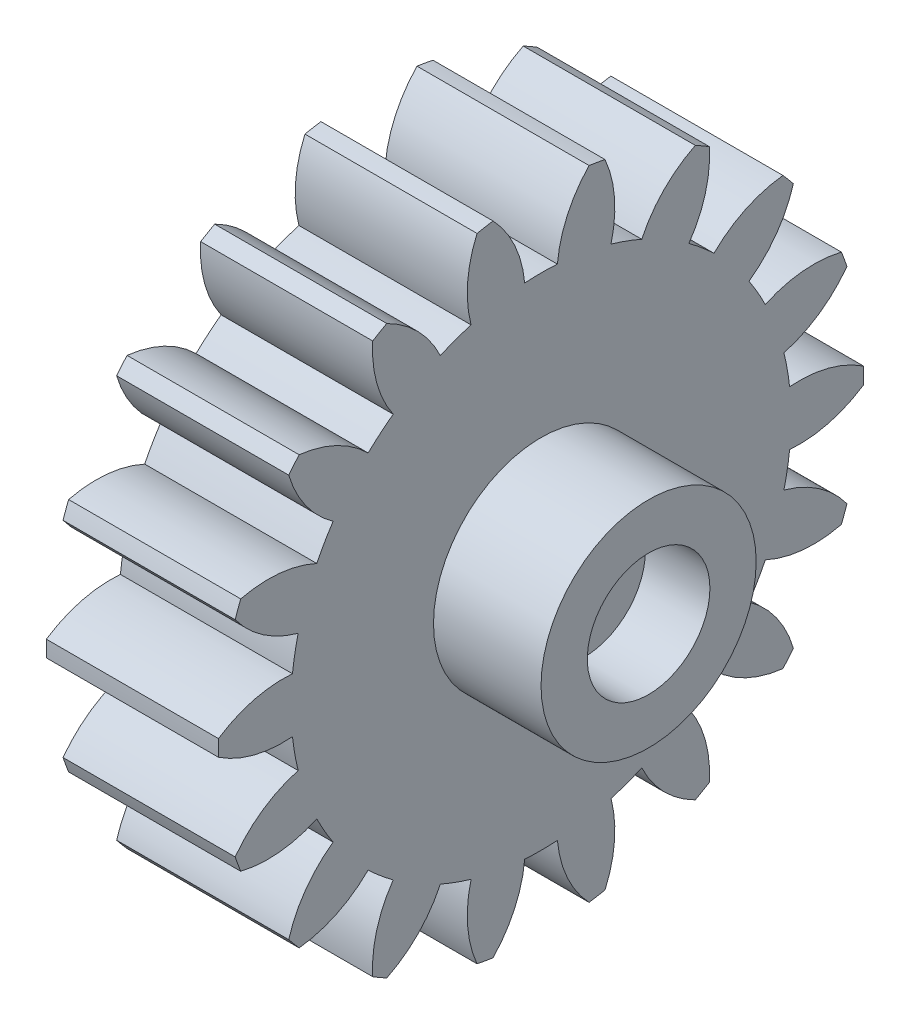
SolidWorks part; units mm, degrees
ref_plane "Plane1" through (0, 0, 0) normal (0, 0, 1) x (1, 0, 0)
ref_plane "Plane2" through (0, 0, 0) normal (0, 1, 0) x (1, 0, 0)
ref_plane "Plane3" through (0, 0, 0) normal (1, 0, 0) x (0, 0, -1)
sketch "HoldingSke" plane through (0, 0, 0) normal (0, 1, 0) x (1, 0, 0)
  line L0 (0, 0) -> (0.634, -0.206)
  line L1 (-15, 0) -> (100, 0) construction
  line L2 (0, 0) -> (-2.1039, 2.3779)
  line L3 (0, 0) -> (-11.863, 4.5341)
  line L4 (0, 0) -> (8.2133, 2.6687)
  line L5 (0, 0) -> (-46.8476, -17.4728)
  line L6 (0, 0) -> (-6.6317, -4.4744)
  line L7 (-2.1039, 2.3779) -> (8.6586, 51.2059)
  line L8 (-76.2, 54.61) -> (-76.1, 54.61)
  line L9 (-71.009, 38.7566) -> (-53.1078, 45.2721)
  line L10 (-76.2, 71.12) -> (104.1128, 71.12)
  line L11 (0, 0) -> (-8, 0)
  line L12 (-76.2, 101.6) -> (-76.147, 101.6)
  line L13 (24.9733, 27.94) -> (52.9518, 28.4284)
  line L14 (24.9733, 27.94) -> (24.9743, 27.94)
  line L15 (24.9733, 27.94) -> (100.4006, 29.5858)
  line L16 (-63.627, -1.5) -> (-12.827, -1.5)
  circle A0 centre (0, 0) radius 0.4
  circle A1 centre (0, 0) radius 11.624
  circle A2 centre (0, 0) radius 37.5
  circle A3 centre (0, 0) radius 0.4
  dimension "MHD" = 23.248
  dimension "Hub_dia" = 75
  dimension "Bore" = 0.8
  dimension "MBD" = 0.8
  dimension "Num_teeth" = 18
  dimension "Pitch" = 0.6667
  dimension "Overall_len" = 50
  dimension "Show_teeth" = 18
  dimension "Thickness" = 8
  dimension "OAL" = 50.0001
  dimension "T_dim" = 0.1
  dimension "Ap" = 20
  dimension "H" = 19.05
  dimension "Pitch_radius" = 180.3128
  dimension "Width" = 8
  dimension "Backlash" = 0.053
  dimension "Addendum_fac" = 1
  dimension "Dedendum_fac" = 1.25
  dimension "Clearance_fac" = 0.25
  dimension "Dedendum_add" = 0.001
  dimension "Module" = 1.5
sketch "BasProSke" plane through (0, 0, 0) normal (0, 1, 0) x (1, 0, 0)
  line L0 (-10, 0) -> (60, 0) construction
  line L1 (0, 0) -> (0, 15)
  line L2 (0, 0) -> (8, 0)
  line L3 (8, 0) -> (8, 15)
  line L4 (8, 15) -> (0, 15)
  dimension "Thickness" = 8
  dimension "Diameter" = 30
revolve "Base-Revolve" add sketch "BasProSke" angle 360 about L0
sketch "TooCutSke" plane through (0, 0, 0) normal (1, 0, 0) x (0, 0, -1)
  line L1 (0, 0) -> (0, 107) construction
  line L2 (0, 0) -> (-1.2693, 13.4402) construction
  line L3 (0, 0) -> (-4.6734, 26.504) construction
  line L4 (-1.2693, 13.4402) -> (-2.3367, 13.252) construction
  arc A0 (0.76, 11.5991) -> (-0.76, 11.5991) centre (0, 0) ccw
  arc A1 (2.2542, 14.8553) -> (-2.2542, 14.8553) centre (0, 0) ccw
  circle A2 centre (0, 0) radius 13.5 construction
  circle A3 centre (0, 0) radius 12.6859 construction
  arc A4 (-0.76, 11.5991) -> (-2.2542, 14.8553) centre (-6.1371, 11.1026) ccw
  arc A5 (2.2542, 14.8553) -> (0.76, 11.5991) centre (6.1371, 11.1026) ccw
  dimension "Root_dia" = 23.248
  dimension "Overcut_dia" = 30.0508
  dimension "Pitch_dia" = 27
  dimension "Base_dia" = 25.3717
  dimension "Flank_rad" = 5.4
  dimension "Half_ang" = 10
  dimension "Half_CT" = 1.0839
extrude "ToothCut" cut sketch "TooCutSke" along normal through all
fillet "Breaks" [suppressed] radius 0.03
fillet "RootFillets" [suppressed] radius 0.376
pattern_circular "TeethCuts" count 18 every 20 about axis through (-10, 0, 0) along (1, 0, 0) of "ToothCut", "RootFillets", "Breaks"
sketch "HubNeaOneSke" plane through (0, 0, 0) normal (-1, 0, 0) x (0, 0, 1)
  circle A0 centre (0, 0) radius 11.624
  dimension "Diameter" = 23.248
extrude "HubNearOne" [suppressed] add sketch "HubNeaOneSke" along normal blind 42.0001
sketch "HubNeaBotSke" plane through (0, 0, 0) normal (-1, 0, 0) x (0, 0, 1)
  circle A0 centre (0, 0) radius 11.624
  dimension "Diameter" = 23.248
extrude "HubNearBoth" [suppressed] add sketch "HubNeaBotSke" along normal blind 21
ref_plane "FarPln" through (8, 0, 0) normal (1, 0, 0) x (0, 0, -1)
sketch "HubFarSke" plane through (8, 0, 0) normal (1, 0, 0) x (0, 0, -1)
  circle A0 centre (0, 0) radius 11.624
  dimension "Diameter" = 23.248
extrude "HubFar" [suppressed] add sketch "HubFarSke" along normal blind 21
sketch "BorSke" plane through (0, 0, 0) normal (1, 0, 0) x (0, 0, -1)
  circle A0 centre (0, 0) radius 0.4
  dimension "Diameter" = 0.8
extrude "Bore" cut sketch "BorSke" along normal mid plane 100.0001
sketch "KeySke" plane through (0, 0, 0) normal (1, 0, 0) x (0, 0, -1)
  line L0 (-0.05, 0) -> (-0.05, 0.5)
  line L1 (-0.05, 0.5) -> (0.05, 0.5)
  line L2 (0.05, 0.5) -> (0.05, 0)
  line L3 (0, 0) -> (0, 34) construction
  line L4 (-0.05, 0) -> (0.05, 0)
  dimension "Offset" = 0.5
  dimension "Width" = 0.1
extrude "Keyway" [suppressed] cut sketch "KeySke" along normal mid plane 100.0001
pattern_circular "Keyway2" [suppressed] count 2 every 90 about axis through (-10, 0, 0) along (1, 0, 0)
sketch "Esquisse1" plane through (8, 0, 0) normal (1, 0, 0) x (0, 0, -1)
  circle A0 centre (0, 0) radius 5
  dimension "D1" = 10
extrude "Boss.-Extru.1" add sketch "Esquisse1" along normal blind 5
sketch "Esquisse2" plane through (13, 0, 0) normal (1, 0, 0) x (0, 0, -1)
  circle A0 centre (0, 0) radius 2.85
  dimension "D1" = 5.7
extrude "Enlèv. mat.-Extru.1" cut sketch "Esquisse2" against normal blind 3
sketch "Esquisse3" plane through (10, 0, 0) normal (1, 0, 0) x (0, 0, -1)
  circle A0 centre (0, 0) radius 1
  dimension "D1" = 2
extrude "Enlèv. mat.-Extru.2" cut sketch "Esquisse3" against normal through all
equation "' \"Module@HoldingSke\" = 6.35"
equation "' \"Num_teeth@HoldingSke\" = 12"
equation "' \"Ap@HoldingSke\" =  20"
equation "' \"Ap@HoldingSke\" = 20"
equation "' \"Width@HoldingSke\" = 0.5 * 25.4"
equation "' \"Hub_dia@HoldingSke\"= 1 * 25.4"
equation "' \"Hub_dia@HoldingSke\" = 1 * 25.4"
equation "' \"Overall_len@HoldingSke\" = 1.0 * 25.4"
equation "' \"Bore@HoldingSke\" = 0.75 * 25.4"
equation "' \"T_dim@HoldingSke\" = 0.1 * 25.4"
equation "' \"Width@KeySke\" = 0.25 * 25.4"
equation "' \"Show_teeth@HoldingSke\" = 13"
equation "' \"Backlash@HoldingSke\" = 0.009 * 25.4"
equation "' \"Addendum_fac@HoldingSke\" = 1.0"
equation "' \"Dedendum_fac@HoldingSke\" = 1.25"
equation "' \"Dedendum_add@HoldingSke\" = 0.00005 * 25.4"
equation "' \"Clearance_fac@HoldingSke\" = 0.25"
equation "\"Pitch@HoldingSke\" = 1 / \"Module@HoldingSke\""
equation "\"Overcut_dia@TooCutSke\" = (\"Num_teeth@HoldingSke\" + 2 * \"Addendum_fac@HoldingSke\") / \"Pitch@HoldingSke\" + 0.002 * 25.4"
equation "\"Pitch_dia@TooCutSke\" = \"Num_teeth@HoldingSke\" / \"Pitch@HoldingSke\""
equation "\"Base_dia@TooCutSke\" = \"Num_teeth@HoldingSke\" / \"Pitch@HoldingSke\" * cos((\"Ap@HoldingSke\"  * 3.14159265 / 180))"
equation "\"Root_dia@TooCutSke\" = (\"Num_teeth@HoldingSke\" + 2) / \"Pitch@HoldingSke\" - 2 * (\"Addendum_fac@HoldingSke\" + \"Dedendum_fac@HoldingSke\") / \"Pitch@HoldingSke\" - \"Dedendum_add@HoldingSke\" * 2"
equation "\"Half_ang@TooCutSke\" = 180 / \"Num_teeth@HoldingSke\""
equation "\"Half_CT@TooCutSke\" = \"Num_teeth@HoldingSke\" / \"Pitch@HoldingSke\" * sin((3.14159265 / 2 / \"Num_teeth@HoldingSke\")) / 2 - 7 * \"Backlash@HoldingSke\" / 4"
equation "\"Flank_rad@TooCutSke\" = \"Num_teeth@HoldingSke\" / \"Pitch@HoldingSke\" / 5"
equation "\"Radius@RootFillets\" = \"Clearance_fac@HoldingSke\" / \"Pitch@HoldingSke\" + \"Dedendum_add@HoldingSke\""
equation "\"Break_rad@Breaks\" = 0.02 / \"Pitch@HoldingSke\""
equation "\"Thickness@HoldingSke\" = \"Width@HoldingSke\""
equation "\"OAL@HoldingSke\" = \"Thickness@HoldingSke\""
equation "\"MHD@HoldingSke\" = (\"Num_teeth@HoldingSke\" + 2) / \"Pitch@HoldingSke\" - 2 * (\"Addendum_fac@HoldingSke\" + \"Dedendum_fac@HoldingSke\")  / \"Pitch@HoldingSke\" - \"Dedendum_add@HoldingSke\" * 2"
equation "\"MBD@HoldingSke\" = (\"Num_teeth@HoldingSke\" + 2) / \"Pitch@HoldingSke\" - 2 * (\"Addendum_fac@HoldingSke\" + \"Dedendum_fac@HoldingSke\")  / \"Pitch@HoldingSke\" - \"Dedendum_add@HoldingSke\" * 2 - 0.002 * 25.4"
equation "\"MHD@HoldingSke\" = ((sgn( \"MHD@HoldingSke\" - \"Hub_dia@HoldingSke\" )-1)*( \"MHD@HoldingSke\" - \"Hub_dia@HoldingSke\" ))/-2+ \"Hub_dia@HoldingSke\""
equation "\"MBD@HoldingSke\" = ((sgn( \"MBD@HoldingSke\" - \"Bore@HoldingSke\" )-1)*( \"MBD@HoldingSke\" - \"Bore@HoldingSke\" ))/-2+ \"Bore@HoldingSke\""
equation "\"OAL@HoldingSke\" = ((sgn( \"OAL@HoldingSke\" - \"Overall_len@HoldingSke\" )+1)*( \"OAL@HoldingSke\" - \"Overall_len@HoldingSke\" ))/2 + \"Overall_len@HoldingSke\" + 0.000002 * 25.4"
equation "\"Num_teeth@TeethCuts\" = int( \"Show_teeth@HoldingSke\" ) + 1"
equation "\"Num_teeth@TeethCuts\" = ((sgn( \"Num_teeth@TeethCuts\" - \"Num_teeth@HoldingSke\" )-1)*( \"Num_teeth@TeethCuts\" - \"Num_teeth@HoldingSke\" ))/-2+ \"Num_teeth@HoldingSke\""
equation "\"Num_teeth@TeethCuts\" = ((sgn( \"Num_teeth@TeethCuts\" - 2.0)+1)*( \"Num_teeth@TeethCuts\" - 2.0))/2 +2.0"
equation "\"Angle@TeethCuts\" = 360.0 / \"Num_teeth@HoldingSke\""
equation "\"Diameter@BasProSke\" = (\"Num_teeth@HoldingSke\" + 2 * \"Addendum_fac@HoldingSke\") / \"Pitch@HoldingSke\""
equation "\"Thickness@BasProSke\"  = \"Thickness@HoldingSke\""
equation "' \"Fillet_rad@BasProSke\" =  \"Thickness@HoldingSke\" * 0.05"
equation "' \"Fillet_rad@BasProSke\" = \"Thickness@HoldingSke\" * 0.05"
equation "\"MHD@HoldingSke\" = ((sgn( \"MHD@HoldingSke\" - \"Root_dia@TooCutSke\" )-1)*( \"MHD@HoldingSke\" - \"Root_dia@TooCutSke\" ))/-2+ \"Root_dia@TooCutSke\""
equation "\"Diameter@HubNeaOneSke\" = \"MHD@HoldingSke\""
equation "\"Length@HubNearOne\" = \"OAL@HoldingSke\" - \"Thickness@BasProSke\""
equation "\"Diameter@HubNeaBotSke\" = \"MHD@HoldingSke\""
equation "\"Length@HubNearBoth\" = ( \"OAL@HoldingSke\" - \"Thickness@BasProSke\" ) / 2.0"
equation "\"Thickness@FarPln\" = \"Thickness@BasProSke\""
equation "\"Diameter@HubFarSke\" = \"MHD@HoldingSke\""
equation "\"Length@HubFar\" = ( \"OAL@HoldingSke\" - \"Thickness@BasProSke\" ) / 2.0"
equation "\"Diameter@BorSke\" = \"MBD@HoldingSke\""
equation "\"D1@Bore\" = \"OAL@HoldingSke\" * 2.0"
equation "\"D1@Keyway\" = \"OAL@HoldingSke\" * 2.0"
equation "\"Offset@KeySke\" = \"T_dim@HoldingSke\" + \"MBD@HoldingSke\" / 2.0"
